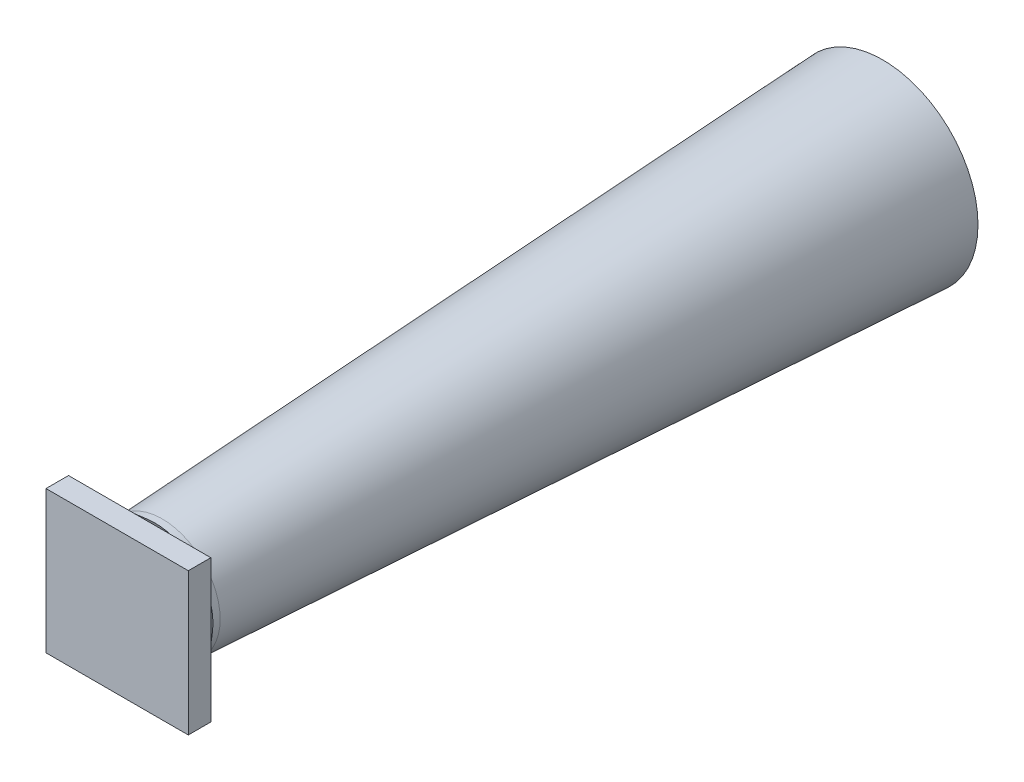
SolidWorks part; units mm, degrees
ref_plane "Front Plane" through (0, 0, 0) normal (0, 0, 1) x (1, 0, 0)
ref_plane "Top Plane" through (0, 0, 0) normal (0, 1, 0) x (1, 0, 0)
ref_plane "Right Plane" through (0, 0, 0) normal (1, 0, 0) x (0, 0, -1)
sketch "Sketch1" plane through (0, 0, 0) normal (0, 0, 1) x (1, 0, 0)
  circle A0 centre (7.8533, -30.8904) radius 1.3217
ref_plane "Plane1" through (0, 0, 10) normal (0, 0, 1) x (1, 0, 0)
sketch "Sketch2" plane through (0, 0, 10) normal (0, 0, 1) x (1, 0, 0)
  circle A0 centre (7.8533, -30.8904) radius 0.8047
loft "Loft1" add profiles "Sketch1", "Sketch2"
sketch "Sketch5" plane through (0, 0, 10) normal (0, 0, 1) x (1, 0, 0)
  circle A1 centre (7.8533, -30.8904) radius 0.8047
  circle A2 centre (7.8533, -30.8904) radius 0.8047
  dimension "D1" = 0
extrude "Boss-Extrude2" add sketch "Sketch5" along normal blind 0.1
sketch "Sketch6" plane through (0, 0, 10.1) normal (0, 0, 1) x (1, 0, 0)
  circle A1 centre (7.8533, -30.8904) radius 0.8047
  circle A2 centre (7.8533, -30.8904) radius 0.8047
  dimension "D1" = 0
ref_plane "Plane2" through (0, 0, 10.3125) normal (0, 0, 1) x (1, 0, 0)
sketch "Sketch7" plane through (0, 0, 10.3125) normal (0, 0, 1) x (1, 0, 0)
  circle A0 centre (7.8533, -30.8904) radius 0.9874
loft "Loft2" add profiles "Sketch6", "Sketch7"
sketch "Sketch8" plane through (0, 0, 10.3125) normal (0, 0, 1) x (1, 0, 0)
  line L1 (6.8659, -31.8779) -> (8.8408, -31.8779)
  line L2 (6.8659, -31.8779) -> (6.8659, -29.903)
  line L3 (6.8659, -29.903) -> (8.8408, -29.903)
  line L4 (8.8408, -31.8779) -> (8.8408, -29.903)
  line L5 (6.8659, -31.8779) -> (8.8408, -29.903) construction
  line L6 (6.8659, -29.903) -> (8.8408, -31.8779) construction
extrude "Boss-Extrude3" add sketch "Sketch8" along normal blind 0.3125
